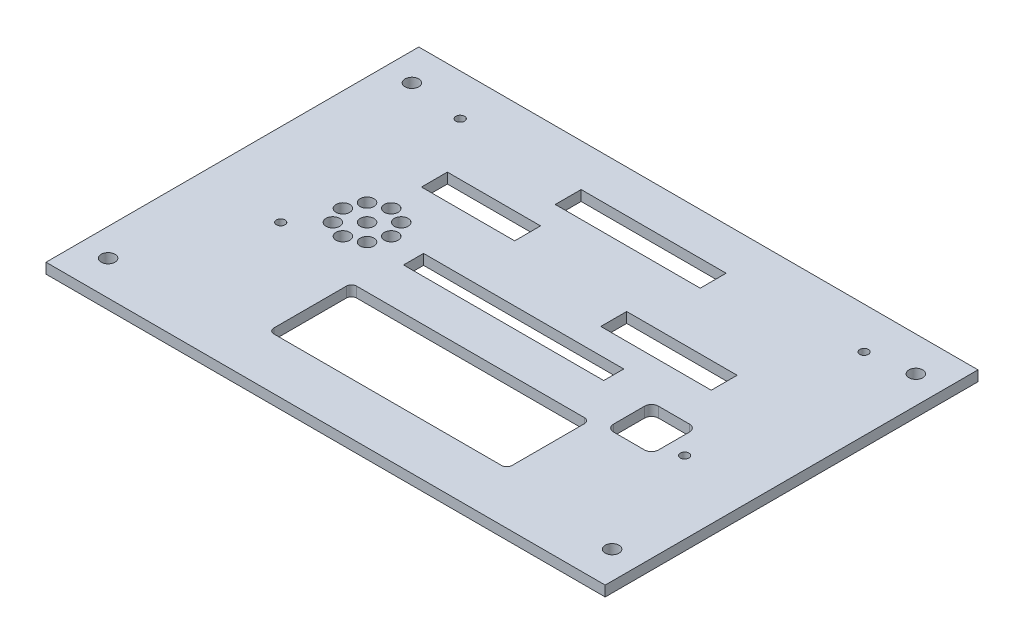
SolidWorks part; units mm, degrees
ref_plane "Спереди" through (0, 0, 0) normal (0, 0, 1) x (1, 0, 0)
ref_plane "Сверху" through (0, 0, 0) normal (0, 1, 0) x (1, 0, 0)
ref_plane "Справа" through (0, 0, 0) normal (1, 0, 0) x (0, 0, -1)
sketch "Эскиз1" plane through (0, 0, 0) normal (0, 1, 0) x (1, 0, 0)
  line L1 (-81, -54) -> (81, -54)
  line L2 (-81, -54) -> (-81, 54)
  line L3 (-81, 54) -> (81, 54)
  line L4 (81, -54) -> (81, 54)
  line L5 (-81, -54) -> (81, 54) construction
  line L6 (-81, 54) -> (81, -54) construction
  dimension "D1" = 162
  dimension "D2" = 108
extrude "Бобышка-Вытянуть1" add sketch "Эскиз1" along normal blind 3
sketch "Эскиз2" plane through (0, 3, 0) normal (0, 1, 0) x (1, 0, 0)
  line L0 (-21.725, 38) -> (20.275, 38) construction
  line L1 (-21.725, 41.75) -> (20.275, 41.75)
  line L2 (-21.725, 41.75) -> (-21.725, 34.25)
  line L3 (-21.725, 34.25) -> (20.275, 34.25)
  line L4 (20.275, 41.75) -> (20.275, 34.25)
  line L5 (-45.475, 26.75) -> (-18.475, 26.75)
  line L6 (-45.475, 26.75) -> (-45.475, 19.25)
  line L7 (-45.475, 19.25) -> (-18.475, 19.25)
  line L8 (-18.475, 26.75) -> (-18.475, 19.25)
  line L9 (15.475, 17.75) -> (47.475, 17.75)
  line L10 (15.475, 17.75) -> (15.475, 10.25)
  line L11 (15.475, 10.25) -> (47.475, 10.25)
  line L12 (47.475, 17.75) -> (47.475, 10.25)
  line L13 (-28.525, 2.9) -> (29.475, 2.9)
  line L14 (-28.525, 2.9) -> (-28.525, -2.9)
  line L15 (-28.525, -2.9) -> (29.475, -2.9)
  line L16 (29.475, 2.9) -> (29.475, -2.9)
  line L17 (-31.5, -15) -> (37.5, -15)
  line L18 (-31.5, -15) -> (-31.5, -39)
  line L19 (-31.5, -39) -> (37.5, -39)
  line L20 (37.5, -15) -> (37.5, -39)
  line L21 (41.816, -1.4) -> (54.816, -1.4)
  line L22 (41.816, -1.4) -> (41.816, -14.4)
  line L23 (41.816, -14.4) -> (54.816, -14.4)
  line L24 (54.816, -1.4) -> (54.816, -14.4)
  line L25 (-0.725, 41.75) -> (-0.725, 34.25) construction
  line L26 (-45.475, 23) -> (-18.475, 23) construction
  line L27 (-31.975, 19.25) -> (-31.975, 26.75) construction
  line L28 (15.475, 14) -> (47.475, 14) construction
  line L29 (31.475, 17.75) -> (31.475, 10.25) construction
  line L30 (-28.525, 0) -> (29.475, 0) construction
  line L31 (0.475, 2.9) -> (0.475, -2.9) construction
  line L32 (81, -54) -> (81, 54) construction
  line L34 (-31.5, -27) -> (37.5, -27) construction
  line L35 (3, -15) -> (3, -39) construction
  circle A0 centre (-72.9995, 44.0001) radius 2
  circle A1 centre (73, 44) radius 2
  circle A2 centre (-73, -44) radius 2
  circle A3 centre (73, -44) radius 2
  point P29 (-0.725, 38)
  point P35 (-31.975, 23)
  point P40 (31.475, 14)
  point P44 (0.475, 0)
  point P48 (48.316, -14.4)
  point P54 (3, -27)
  point P63 (41.816, -7.9)
  dimension "D26" = 4
  dimension "D27" = 4
  dimension "D28" = 4
  dimension "D29" = 4
  dimension "D1" = 3.75
  dimension "D3" = 42
  dimension "D4" = 27
  dimension "D5" = 3.75
  dimension "D6" = 31.975
  dimension "D7" = 23
  dimension "D8" = 0.725
  dimension "D9" = 32
  dimension "D10" = 3.75
  dimension "D11" = 31.475
  dimension "D12" = 14
  dimension "D13" = 58
  dimension "D14" = 2.9
  dimension "D15" = 0.475
  dimension "D16" = 0
  dimension "D17" = 32.684
  dimension "D18" = 13
  dimension "D19" = 12
  dimension "D20" = 69
  dimension "D21" = 7.9
  dimension "D22" = 3
  dimension "D24" = 27
  dimension "D25" = 38
  dimension "D30" = 72.9995
  dimension "D31" = 44.0001
  dimension "D32" = 73
  dimension "D33" = 44
  dimension "D34" = 73
  dimension "D35" = 44
  dimension "D36" = 44
  dimension "D37" = 73
extrude "Основные отверстия" cut sketch "Эскиз2" against normal through all
fillet "Скругление1" radius 1.5 4 edges at (37.5, 1.5, 39) (37.5, 1.5, 15) (-31.5, 1.5, 39) (-31.5, 1.5, 15)
sketch "Эскиз3" plane through (0, 3, 0) normal (0, 1, 0) x (1, 0, 0)
  line L0 (81, 54) -> (-81, 54) construction
  line L1 (-81, 54) -> (-81, -54) construction
  circle A0 centre (-57, 42) radius 1.25
  circle A1 centre (-57, -10) radius 1.25
  circle A2 centre (60, 42) radius 1.25
  circle A3 centre (60, -10) radius 1.25
  dimension "D1" = 12
  dimension "D2" = 2.5
  dimension "D3" = 24
  dimension "D4" = 52
  dimension "D5" = 117
extrude "Крепление платы" cut sketch "Эскиз3" against normal through all
sketch "Эскиз4" plane through (0, 3, 0) normal (0, 1, 0) x (1, 0, 0)
  line L2 (-81, 54) -> (-81, -54) construction
  line L4 (-81, -54) -> (81, -54) construction
  circle A9 centre (-44.5, 2.51) radius 2
  circle A10 centre (-51.5, 2.51) radius 2
  circle A11 centre (-49.4497, 7.4597) radius 2
  circle A12 centre (-44.5, 9.51) radius 2
  circle A13 centre (-39.5503, 7.4597) radius 2
  circle A14 centre (-37.5, 2.51) radius 2
  circle A15 centre (-39.5503, -2.4397) radius 2
  circle A16 centre (-44.5, -4.49) radius 2
  circle A17 centre (-49.4497, -2.4397) radius 2
  point P45 (-44.5, 2.51)
  dimension "D22" = 36.5
  dimension "D24" = 4
  dimension "D25" = 7
  dimension "D23" = 56.51
  dimension "D26" = 8
extrude "Динамик" cut sketch "Эскиз4" against normal through all
fillet "Скругление2" radius 2 4 edges at (41.816, 1.5, 14.4) (54.816, 1.5, 14.4) (54.816, 1.5, 1.4) (41.816, 1.5, 1.4)
